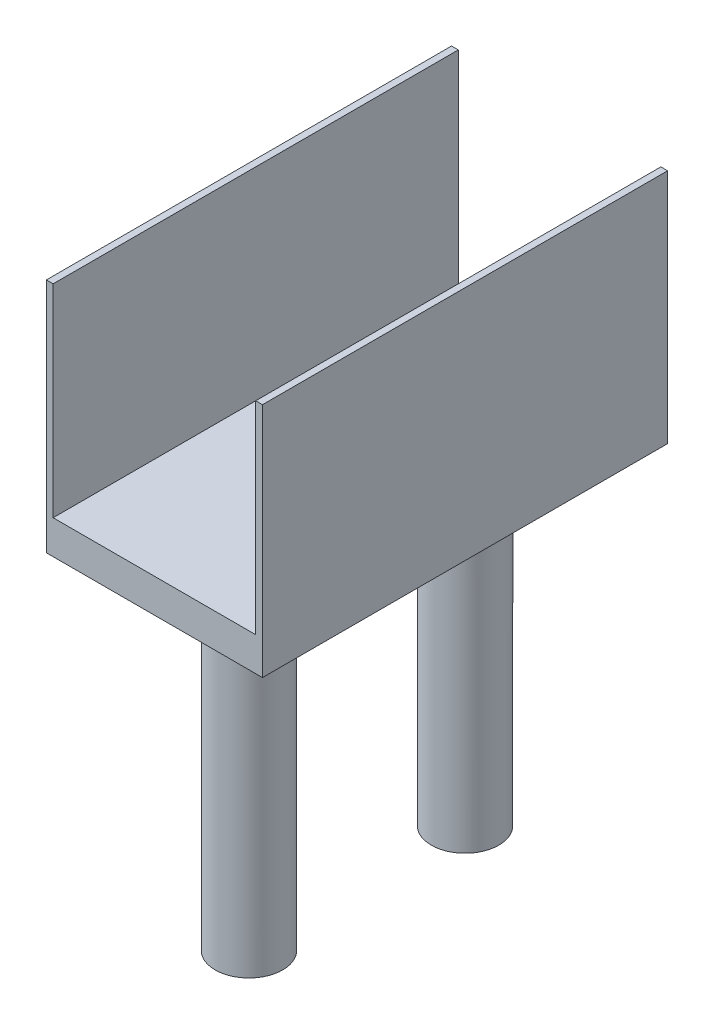
SolidWorks part; units mm, degrees
ref_plane "Front Plane" through (0, 0, 0) normal (0, 0, 1) x (1, 0, 0)
ref_plane "Top Plane" through (0, 0, 0) normal (0, 1, 0) x (1, 0, 0)
ref_plane "Right Plane" through (0, 0, 0) normal (1, 0, 0) x (0, 0, -1)
sketch "Sketch1" plane through (0, 0, 0) normal (0, 1, 0) x (1, 0, 0)
  line L1 (-16, 30) -> (16, 30)
  line L2 (-16, 30) -> (-16, -30)
  line L3 (-16, -30) -> (16, -30)
  line L4 (16, 30) -> (16, -30)
  line L5 (-16, 30) -> (16, -30) construction
  line L6 (-16, -30) -> (16, 30) construction
  point P0 (0, 0)
  dimension "D1" = 60
  dimension "D2" = 32
extrude "Boss-Extrude1" add sketch "Sketch1" along normal mid plane 5
sketch "Sketch2" plane through (0, -2.5, 0) normal (0, -1, 0) x (1, 0, 0)
  line L0 (17.4755, 0) -> (-17.4755, 0) construction
  circle A0 centre (0, 16) radius 5
  circle A1 centre (0, -16) radius 5
  point P10 (0, 0)
  dimension "D1" = 10
  dimension "D2" = 16
extrude "Boss-Extrude2" add sketch "Sketch2" along normal blind 50
sketch "Sketch3" plane through (0, 2.5, 0) normal (0, 1, 0) x (1, 0, 0)
  line L0 (-16, -30) -> (16, -30) construction
  line L1 (-16, 30) -> (-15, 30)
  line L2 (-16, 30) -> (-16, -30)
  line L3 (-16, -30) -> (-15, -30)
  line L4 (-15, 30) -> (-15, -30)
  line L5 (-16, 30) -> (-15, -30) construction
  line L6 (-16, -30) -> (-15, 30) construction
  line L7 (16, 30) -> (-16, 30) construction
  line L8 (16, -30) -> (15, -30)
  line L9 (16, -30) -> (16, 30)
  line L10 (16, 30) -> (15, 30)
  line L11 (15, -30) -> (15, 30)
  line L12 (16, -30) -> (15, 30) construction
  line L13 (16, 30) -> (15, -30) construction
  line L14 (0, -30) -> (0, 30) construction
  point P4 (-15.5, 0)
  point P12 (15.5, 0)
  point P22 (0, 0)
  dimension "D1" = 1
extrude "Boss-Extrude3" add sketch "Sketch3" along normal blind 30
